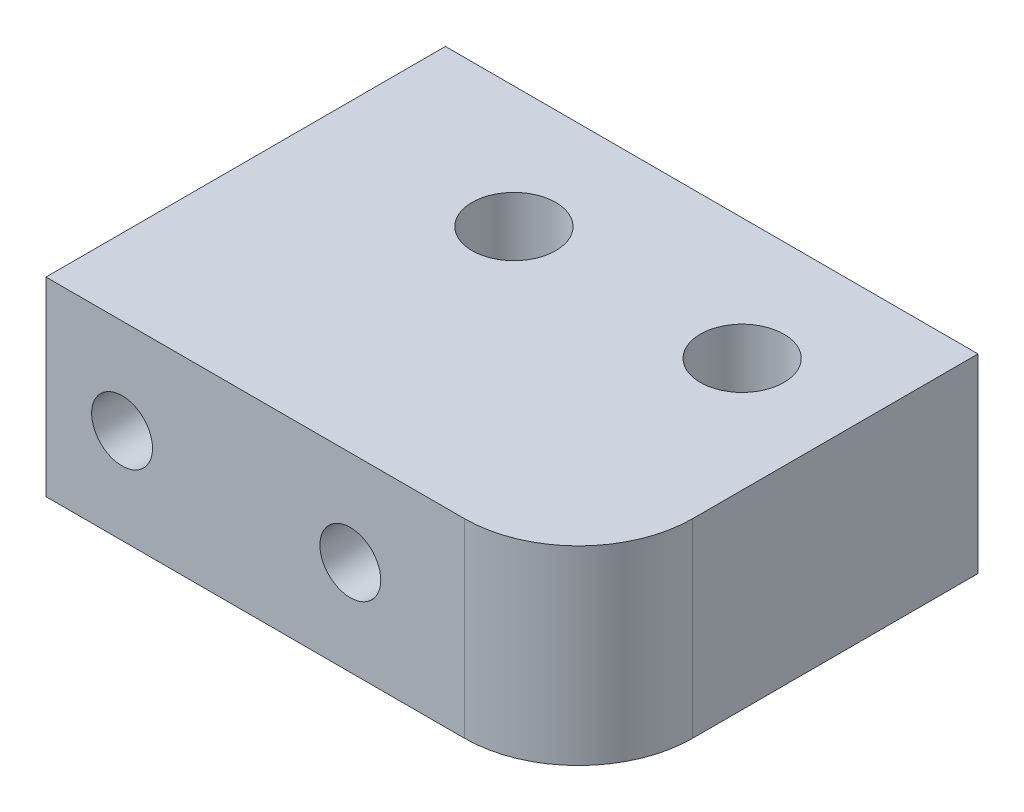
SolidWorks part; units mm, degrees
material "ﾎﾟﾘｵｷｼﾒﾁﾚﾝ(POM)ｱｾﾀｰﾙ共重合体"
ref_plane "正面" through (0, 0, 0) normal (0, 0, 1) x (1, 0, 0)
ref_plane "平面" through (0, 0, 0) normal (0, 1, 0) x (1, 0, 0)
ref_plane "右側面" through (0, 0, 0) normal (1, 0, 0) x (0, 0, -1)
sketch "Sketch1" plane through (0, 0, 0) normal (0, 1, 0) x (1, 0, 0)
  line L1 (-7, 5.25) -> (7, 5.25)
  line L2 (-7, 5.25) -> (-7, -5.25)
  line L3 (-7, -5.25) -> (7, -5.25)
  line L4 (7, 5.25) -> (7, -5.25)
  line L5 (-7, 5.25) -> (7, -5.25) construction
  line L6 (-7, -5.25) -> (7, 5.25) construction
  point P0 (0, 0)
  dimension "D1" = 10.5
  dimension "D2" = 14
extrude "Boss-Extrude1" add sketch "Sketch1" along normal blind 5
sketch "Sketch2" plane through (0, 0, 5.25) normal (0, 0, 1) x (1, 0, 0)
  line L1 (-7, 5) -> (-5, 5)
  line L2 (-7, 5) -> (-7, 2.5)
  line L3 (-7, 2.5) -> (-5, 2.5)
  line L4 (-5, 5) -> (-5, 2.5)
  line L5 (7, 5) -> (1, 5)
  line L6 (7, 5) -> (7, 2.5)
  line L7 (7, 2.5) -> (1, 2.5)
  line L8 (1, 5) -> (1, 2.5)
  dimension "D1" = 2
  dimension "D2" = 2.5
  dimension "D3" = 8
  dimension "D4" = 2.5
sketch "Sketch6" plane through (0, 5, 0) normal (0, 1, 0) x (1, 0, 0)
  line L1 (-7, 5.25) -> (-2, 5.25)
  line L2 (-7, 5.25) -> (-7, 2.25)
  line L3 (-7, 2.25) -> (-2, 2.25)
  line L4 (-2, 5.25) -> (-2, 2.25)
  line L5 (7, 5.25) -> (4, 5.25)
  line L6 (7, 5.25) -> (7, 2.25)
  line L7 (7, 2.25) -> (4, 2.25)
  line L8 (4, 5.25) -> (4, 2.25)
  dimension "D1" = 5
  dimension "D2" = 11
  dimension "D3" = 3
  dimension "D4" = 3
hole_wizard "Hole1" positions "Sketch8" profile "Sketch9" legacy end condition through all
sketch "Sketch8" plane through (0, 0, 0) normal (0, 1, 0) x (1, 0, 0)
  line L0 (7, 5.25) -> (-7, 5.25) construction
  point P0 (-2, 2.05)
  point P3 (4, 2.05)
  dimension "D1" = 3.2
  dimension "D2" = 3.2
sketch "Sketch9" plane through (-2, 0, -2.05) normal (1, 0, 0) x (0, 0, -1)
  line L0 (0, 0) -> (0, 5)
  line L1 (0, 5) -> (1.1, 5)
  line L2 (1.1, 5) -> (1.1, 1.3)
  line L3 (1.1, 1.3) -> (2.1, 1.3)
  line L4 (2.1, 1.3) -> (2.1, 0)
  line L5 (2.1, 0) -> (0, 0)
  line L6 (0, 110) -> (0, -10) construction
  dimension "Diameter" = 2.2
  dimension "Depth" = 5
  dimension "C-Bore Diameter" = 4.2
  dimension "C-Bore Depth" = 1.3
fillet "ﾌｨﾚｯﾄ2" radius 3 1 edges at (7, 2.5, 5.25)
sketch "ｽｹｯﾁ6" plane through (0, 0, 5.25) normal (0, 0, 1) x (1, 0, 0)
  line L0 (-7, 5) -> (-7, 0) construction
  line L1 (-7, 0) -> (4, 0) construction
  point P0 (-5, 2.5)
  point P1 (1, 2.5)
  dimension "D1" = 2
  dimension "D2" = 8
  dimension "D3" = 2.5
  dimension "D4" = 2.5
hole_wizard "M2x0.4 ねじ穴5" positions "3Dｽｹｯﾁ4" profile "ｽｹｯﾁ7" tap size "M2x0.4" standard "JIS" end condition through all
sketch3d "3Dｽｹｯﾁ4"
  point P0 (-5, 2.5, 5.25)
  point P3 (1, 2.5, 5.25)
sketch "ｽｹｯﾁ7" plane through (-5, 2.5, 5.25) normal (1, 0, 0) x (0, -1, 0)
  line L0 (0, 0) -> (0, 10.5)
  line L1 (0, 10.5) -> (0.8, 10.5)
  line L2 (0.8, 10.5) -> (0.8, 0)
  line L5 (0.8, 0) -> (0, 0)
  line L11 (0, -6.35) -> (0, 107.95) construction
  dimension "次ｻｰﾌｪｽまでのねじ下穴ﾄﾞﾘﾙ直径" = 1.6
  dimension "次ｻｰﾌｪｽまでのねじ下穴ﾄﾞﾘﾙの深さ" = 10.5
cosmetic thread "穴のねじ山5" parameters "D1"=10.5, "D2"=2
cosmetic thread "穴のねじ山6" parameters "D1"=10.5, "D2"=2
sketch "Sketch11" plane through (0, 5, 0) normal (0, 1, 0) x (1, 0, 0)
  point P0 (-2, 2.05)
  point P1 (4, 2.05)
